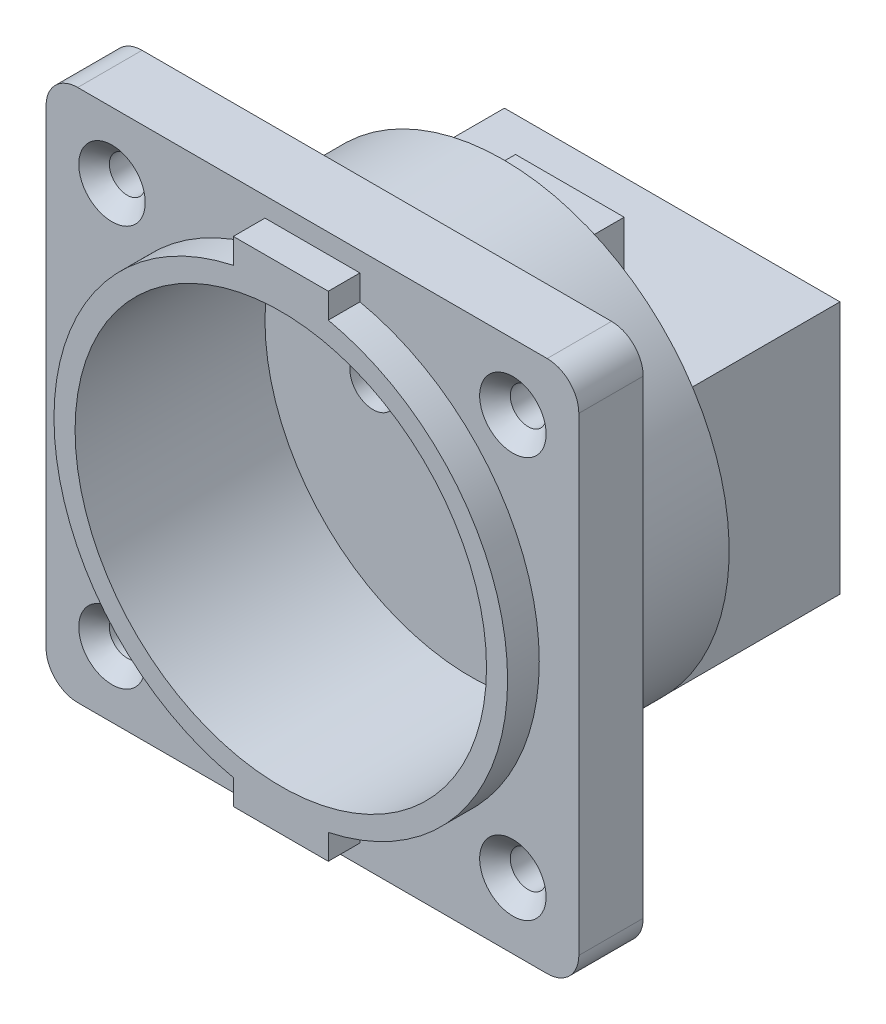
SolidWorks part; units mm, degrees
material "ABS"
ref_plane "Ebene vorne" through (0, 0, 0) normal (0, 0, 1) x (1, 0, 0)
ref_plane "Ebene oben" through (0, 0, 0) normal (0, 1, 0) x (1, 0, 0)
ref_plane "Ebene rechts" through (0, 0, 0) normal (1, 0, 0) x (0, 0, -1)
sketch "Skizze1" plane through (0, 0, 0) normal (0, 0, 1) x (1, 0, 0)
  line L1 (-25.25, -25.25) -> (25.25, -25.25)
  line L2 (-25.25, -25.25) -> (-25.25, 25.25)
  line L3 (-25.25, 25.25) -> (25.25, 25.25)
  line L4 (25.25, -25.25) -> (25.25, 25.25)
  line L5 (-25.25, -25.25) -> (25.25, 25.25) construction
  line L6 (-25.25, 25.25) -> (25.25, -25.25) construction
  point P0 (0, 0)
  dimension "D1" = 50.5
  dimension "D2" = 50.5
extrude "Aufsatz-Linear austragen1" add sketch "Skizze1" along normal blind 6.1
sketch "Skizze2" plane through (0, 0, 6.1) normal (0, 0, 1) x (1, 0, 0)
  line L0 (0, 23.4) -> (0, 0) construction
  line L1 (-4.5, 23.4) -> (4.5, 23.4)
  line L2 (-4.5, 23.4) -> (-4.5, -23.4)
  line L3 (-4.5, -23.4) -> (4.5, -23.4)
  line L4 (4.5, 23.4) -> (4.5, -23.4)
  line L5 (0, 0) -> (0, -23.4) construction
  circle A0 centre (0, 0) radius 21.5
  dimension "D1" = 43
  dimension "D2" = 9
  dimension "D3" = 46.8
extrude "Aufsatz-Linear austragen2" add sketch "Skizze2" along normal blind 3 contours L2 A0 | L4 A0 L2 | L4 A0 | A0 L4 L1 L2 | A0 L2 L3 L4
sketch "Skizze3" plane through (0, 0, 0) normal (0, 0, -1) x (-1, 0, 0)
  circle A0 centre (0, 0) radius 21.4
  dimension "D1" = 42.8
extrude "Aufsatz-Linear austragen3" add sketch "Skizze3" along normal blind 12
sketch "Skizze4" plane through (0, 0, -12) normal (0, 0, -1) x (-1, 0, 0)
  line L0 (0, 0) -> (0, 9.6769) construction
  line L1 (-15.9, 9.6769) -> (15.9, 9.6769)
  line L2 (-15.9, 9.6769) -> (-15.9, -14.3231)
  line L3 (-15.9, -14.3231) -> (15.9, -14.3231)
  line L4 (15.9, 9.6769) -> (15.9, -14.3231)
  circle A0 centre (0, 0) radius 21.4 construction
  dimension "D1" = 31.8
  dimension "D2" = 24
extrude "Aufsatz-Linear austragen4" add sketch "Skizze4" along normal blind 16
hole_wizard "Formsenkung für M3 Linsensenkschraube mit Schlitz1" positions "Skizze5" profile "Skizze6" countersink size "M3" standard "DIN" end condition through all
sketch "Skizze5" plane through (0, 0, 6.1) normal (0, 0, 1) x (1, 0, 0)
  line L0 (-19, 19) -> (19, 19) construction
  line L1 (19, 19) -> (19, -19) construction
  line L2 (19, -19) -> (-19, -19) construction
  line L3 (-19, -19) -> (-19, 19) construction
  line L5 (0, 19) -> (0, 0) construction
  line L6 (0, 0) -> (0, -19) construction
  point P0 (-19, 19)
  point P2 (19, 19)
  point P4 (19, -19)
  point P6 (-19, -19)
  dimension "D1" = 38
sketch "Skizze6" plane through (-19, 19, 6.1) normal (1, 0, 0) x (0, -1, 0)
  line L0 (0, 0) -> (0, 34.1)
  line L1 (0, 34.1) -> (1.7, 34.1)
  line L2 (1.7, 34.1) -> (1.7, 1.45)
  line L3 (1.7, 1.45) -> (3.15, 0)
  line L5 (3.15, 0) -> (0, 0)
  line L6 (-1.7, 1.45) -> (-3.15, 0) construction
  line L11 (0, -6.35) -> (0, 107.95) construction
  dimension "Bohrerdurchmesser" = 3.4
  dimension "Bohrungstiefe" = 34.1
  dimension "Senkdurchmesser (Oben)" = 6.3
  dimension "Senkwinkel (Oben)" = 90
fillet "Verrundung1" radius 3 4 edges at (25.25, -25.25, 3.05) (25.25, 25.25, 3.05) (-25.25, -25.25, 3.05) (-25.25, 25.25, 3.05)
sketch "Skizze7" plane through (0, 0, 9.1) normal (0, 0, 1) x (1, 0, 0)
  circle A0 centre (0, 0) radius 19.5
  dimension "D1" = 39
extrude "Schnitt-Linear austragen1" cut sketch "Skizze7" against normal blind 18
hole_wizard "Ø4.4 (4.4) Durchmesser Bohrung1" positions "Skizze8" profile "Skizze9" hole size "Ø4.4" standard "DIN" end condition through all
sketch "Skizze8" plane through (0, 0, -8.9) normal (0, 0, 1) x (1, 0, 0)
  line L0 (-9.25, 0) -> (0, 0) construction
  line L1 (0, 0) -> (9.25, 0) construction
  point P0 (-9.25, 0)
  point P2 (9.25, 0)
  dimension "D1" = 18.5
sketch "Skizze9" plane through (-9.25, 0, -8.9) normal (1, 0, 0) x (0, -1, 0)
  line L0 (0, 0) -> (0, 19.1)
  line L1 (0, 19.1) -> (2.2, 19.1)
  line L2 (2.2, 19.1) -> (2.2, 0)
  line L5 (2.2, 0) -> (0, 0)
  line L11 (0, -6.35) -> (0, 107.95) construction
  dimension "Bohrerdurchmesser" = 4.4
  dimension "Bohrungstiefe" = 19.1
sketch "Skizze10" plane through (0, 0, -12) normal (0, 0, -1) x (-1, 0, 0)
  line L0 (15.9, 9.6769) -> (-15.9, 9.6769) construction
  line L1 (5.15, 16.1) -> (-5.15, 16.1)
  line L2 (5.15, 16.1) -> (5.15, 9.6769)
  line L3 (5.15, 9.6769) -> (-5.15, 9.6769)
  line L4 (-5.15, 16.1) -> (-5.15, 9.6769)
  line L5 (0, 0) -> (0, 9.6769) construction
  line L6 (0, 16.1) -> (0, 21.4) construction
  arc A0 (15.9, -14.3231) -> (-15.9, -14.3231) centre (0, 0) ccw construction
  dimension "D1" = 5.3
  dimension "D2" = 10.3
extrude "Aufsatz-Linear austragen5" add sketch "Skizze10" along normal blind 6.3
